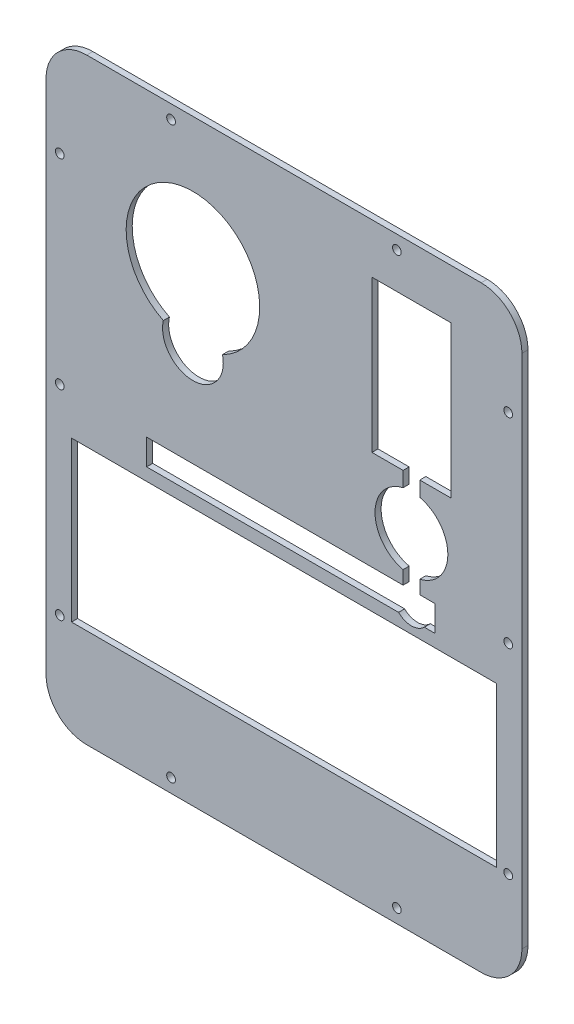
SolidWorks part; units mm, degrees
ref_plane "Front Plane" through (0, 0, 0) normal (1, 0, 0) x (0, 1, 0)
ref_plane "Top Plane" through (0, 0, 0) normal (0, 0, 1) x (0, 1, 0)
ref_plane "Right Plane" through (0, 0, 0) normal (0, 1, 0) x (-1, 0, 0)
sketch "Sketch1" plane through (0, 0, 0) normal (0, 0, 1) x (0, 1, 0)
  line L5 (-107.9246, -99.568) -> (107.9246, -99.568)
  line L6 (-124.968, -82.5246) -> (-124.968, 82.5246)
  line L7 (-107.9246, 99.568) -> (107.9246, 99.568)
  line L8 (124.968, -82.5246) -> (124.968, 82.5246)
  arc A0 (-124.968, 82.5246) -> (-107.9246, 99.568) centre (-107.9246, 82.5246) cw
  arc A1 (-107.9246, -99.568) -> (-124.968, -82.5246) centre (-107.9246, -82.5246) cw
  arc A2 (107.9246, -99.568) -> (124.968, -82.5246) centre (107.9246, -82.5246) ccw
  arc A3 (107.9246, 99.568) -> (124.968, 82.5246) centre (107.9246, 82.5246) cw
  point P15 (124.968, 0)
  point P20 (0, 99.568)
  dimension "D1" = 17.0434
  dimension "D2" = 199.136
  dimension "D3" = 249.936
extrude "Boss-Extrude1" add sketch "Sketch1" along normal blind 2.54
sketch "Sketch2" plane through (0, 0, 2.54) normal (0, 0, 1) x (1, 0, 0)
  line L0 (0, 223.1681) -> (0, -217.0396) construction
  line L1 (-162.9401, 0) -> (143.5585, 0) construction
  line L2 (99.568, -107.9246) -> (99.568, 107.9246) construction
  line L3 (-99.568, 107.9246) -> (-99.568, -107.9246) construction
  line L4 (-82.5246, -124.968) -> (82.5246, -124.968) construction
  point P0 (93.8276, 0)
  point P6 (-93.8276, 0)
  point P7 (47.244, -119.2276)
  point P8 (-47.244, -119.2276)
  point P9 (93.8276, -83.6676)
  point P10 (-93.8276, -83.6676)
  point P22 (-93.8276, 83.6676)
  point P23 (93.8276, 83.6676)
  point P24 (-47.244, 119.2276)
  point P25 (47.244, 119.2276)
  dimension "D1" = 52.324
  dimension "D2" = 52.324
  dimension "D3" = 5.7404
  dimension "D4" = 5.7404
  dimension "D5" = 5.7404
  dimension "D6" = 41.3004
sketch "Sketch6" plane through (0, 0, 2.54) normal (0, 0, 1) x (1, 0, 0)
  line L0 (53.34, 139.097) -> (53.34, -37.7787) construction
  line L3 (-38.1, 127.2984) -> (-38.1, 26.2104) construction
  line L4 (49.8475, 4.6918) -> (49.8475, -0.9525)
  line L20 (-114.4724, 69.85) -> (19.4395, 69.85) construction
  line L21 (-38.1, 69.85) -> (-38.1, 107.4547) construction
  line L22 (-162.9401, 0) -> (143.5585, 0) construction
  line L23 (56.8325, 4.6918) -> (56.8325, -0.9525)
  line L25 (117.4238, 79.5655) -> (-13.9103, 79.5655) construction
  line L28 (49.8475, 40.64) -> (49.8475, 34.3607)
  line L35 (56.8325, 40.64) -> (56.8325, 34.3607)
  line L49 (0, 223.1681) -> (0, -217.0396) construction
  line L51 (36.83, 104.14) -> (69.85, 104.14)
  line L52 (36.83, 104.14) -> (36.83, 40.64)
  line L53 (36.83, 40.64) -> (49.8475, 40.64)
  line L54 (69.85, 104.14) -> (69.85, 40.64)
  line L56 (56.8325, 40.64) -> (69.85, 40.64)
  line L60 (82.8638, -6.35) -> (-86.4031, -6.35) construction
  line L61 (63.1825, -11.7475) -> (58.7188, -11.7475)
  line L62 (-57.4675, -11.7475) -> (-57.4675, -0.9525)
  line L63 (-57.4675, -0.9525) -> (49.8475, -0.9525)
  line L64 (56.8325, -0.9525) -> (63.1825, -0.9525)
  line L65 (63.1825, -0.9525) -> (63.1825, -11.7475)
  line L66 (47.9612, -11.7475) -> (-57.4675, -11.7475)
  arc A16 (-25.7323, 44.7964) -> (-50.4677, 44.7964) centre (-38.1, 69.85) ccw
  arc A17 (-50.4677, 44.7964) -> (-25.7323, 44.7964) centre (-38.1, 41.91) ccw
  arc A18 (56.8325, 4.6918) -> (56.8325, 34.3607) centre (53.34, 19.5262) ccw
  arc A19 (49.8475, 34.3607) -> (49.8475, 4.6918) centre (53.34, 19.5262) ccw
  arc A20 (47.9612, -11.7475) -> (58.7188, -11.7475) centre (53.34, -6.35) ccw
  dimension "D12" = 55.88
  dimension "D13" = 25.4
  dimension "D6" = 30.48
  dimension "D22" = 15.24
  dimension "D11" = 69.85
  dimension "D14" = 38.1
  dimension "D3" = 53.34
  dimension "D5" = 79.5655
  dimension "D15" = 63.5
  dimension "D16" = 33.02
  dimension "D17" = 40.64
  dimension "D18" = 16.51
  dimension "D7" = 3.4925
  dimension "D8" = 3.4925
  dimension "D19" = 21.1137
  dimension "D20" = 46.99
  dimension "D4" = 5.3975
  dimension "D10" = 5.3975
  dimension "D9" = 6.35
  dimension "D21" = 120.65
extrude "Cut-Extrude1" cut sketch "Sketch6" against normal through all
sketch "Sketch7" plane through (0, 0, 2.54) normal (0, 0, 1) x (1, 0, 0)
  line L0 (-82.5246, -124.968) -> (82.5246, -124.968) construction
  line L1 (-88.9, -17.018) -> (88.9, -17.018)
  line L2 (-88.9, -17.018) -> (-88.9, -83.693)
  line L3 (-88.9, -83.693) -> (88.9, -83.693)
  line L4 (88.9, -17.018) -> (88.9, -83.693)
  line L5 (0, 223.1681) -> (0, -217.0396) construction
  point P8 (0, -83.693)
  dimension "D1" = 66.675
  dimension "D2" = 177.8
  dimension "D3" = 41.275
extrude "Cut-Extrude2" cut sketch "Sketch7" against normal through all
hole_wizard "#27 (0.144) Diameter Hole1" positions "Sketch2" profile "Sketch8" hole size "#27" standard "ANSI Inch" end condition through all
sketch "Sketch8" plane through (93.8276, 0, 2.54) normal (1, 0, 0) x (0, -1, 0)
  line L0 (0, 0) -> (0, 2.54)
  line L1 (0, 2.54) -> (1.8288, 2.54)
  line L2 (1.8288, 2.54) -> (1.8288, 0)
  line L5 (1.8288, 0) -> (0, 0)
  line L11 (0, -6.35) -> (0, 107.95) construction
  dimension "Thru Hole Dia." = 3.6576
  dimension "Thru Hole Depth" = 2.54
equation "\"D8@Sketch6\"=\"D7@Sketch6\""
equation "\"D10@Sketch6\"=\"D4@Sketch6\""
